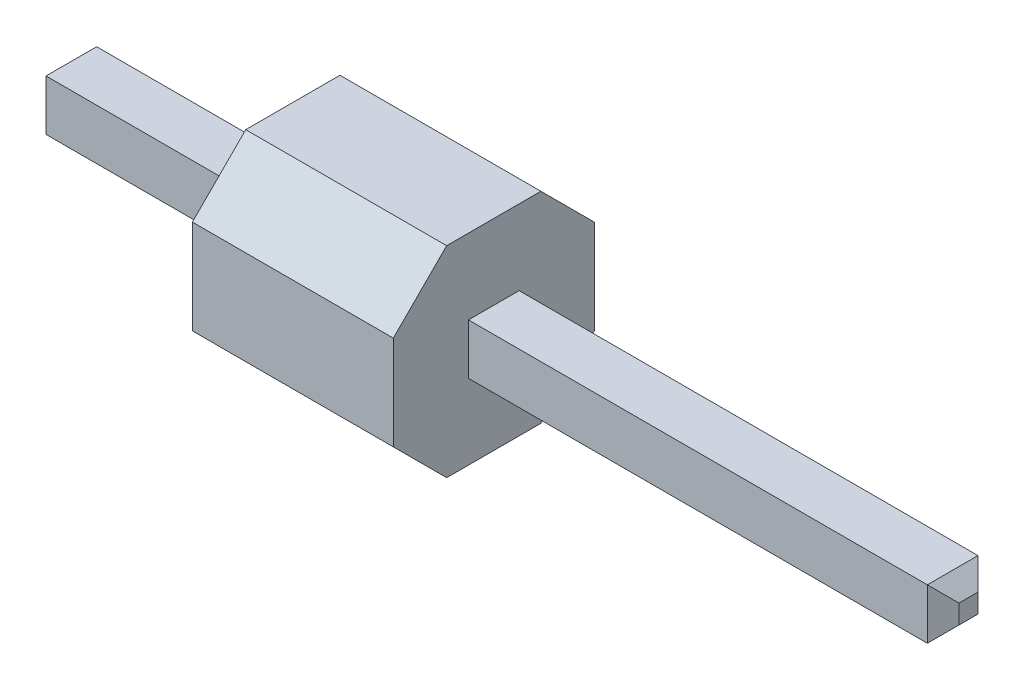
SolidWorks part; units mm, degrees
ref_plane "Alzado" through (0, 0, 0) normal (0, 0, 1) x (1, 0, 0)
ref_plane "Planta" through (0, 0, 0) normal (0, 1, 0) x (1, 0, 0)
ref_plane "Vista lateral" through (0, 0, 0) normal (1, 0, 0) x (0, 0, -1)
sketch "Croquis1" plane through (0, 0, 0) normal (1, 0, 0) x (0, 0, -1)
  line L0 (-0.5955, 1.27) -> (-1.27, 0.5955)
  line L1 (0.5955, 1.27) -> (-0.5955, 1.27)
  line L2 (1.27, 0.5955) -> (1.27, -0.5955)
  line L3 (0.5955, -1.27) -> (-0.5955, -1.27)
  line L4 (-1.27, 0.5955) -> (-1.27, -0.5955)
  line L5 (1.27, 1.27) -> (-1.27, -1.27) construction
  line L6 (1.27, -1.27) -> (-1.27, 1.27) construction
  line L7 (-0.5955, -1.27) -> (-1.27, -0.5955)
  line L8 (1.27, -0.5955) -> (0.5955, -1.27)
  line L9 (1.27, 0.5955) -> (0.5955, 1.27)
  line L12 (0, 0) -> (0, 2.4434) construction
  line L13 (1.27, 0.5955) -> (1.27, 2.4434) construction
  line L22 (0.32, 0.32) -> (-0.32, 0.32)
  line L23 (0.32, 0.32) -> (0.32, -0.32)
  line L24 (0.32, -0.32) -> (-0.32, -0.32)
  line L25 (-0.32, 0.32) -> (-0.32, -0.32)
  line L26 (0.32, 0.32) -> (-0.32, -0.32) construction
  line L27 (0.32, -0.32) -> (-0.32, 0.32) construction
  point P0 (0, 0)
  dimension "D1" = 2.54
  dimension "D2" = 2.54
  dimension "D4" = 0.64
  dimension "D5" = 0.64
extrude "Saliente-Extruir1" add sketch "Croquis1" along normal blind 2.54
sketch "Croquis3" plane through (0, 0, 0) normal (1, 0, 0) x (0, 0, -1)
  line L1 (-0.32, -0.32) -> (0.32, -0.32)
  line L2 (-0.32, -0.32) -> (-0.32, 0.32)
  line L3 (-0.32, 0.32) -> (0.32, 0.32)
  line L4 (0.32, -0.32) -> (0.32, 0.32)
extrude "Saliente-Extruir2" add sketch "Croquis3" along normal blind 8.54 and the other way blind 3 separate body
chamfer "Chaflán1" distance 0.2 angle 45 8 edges at (-3, -0.32, 0) (-3, 0, -0.32) (-3, 0.32, 0) (-3, 0, 0.32) (8.54, 0.32, 0) (8.54, 0, -0.32) (8.54, -0.32, 0) (8.54, 0, 0.32)
